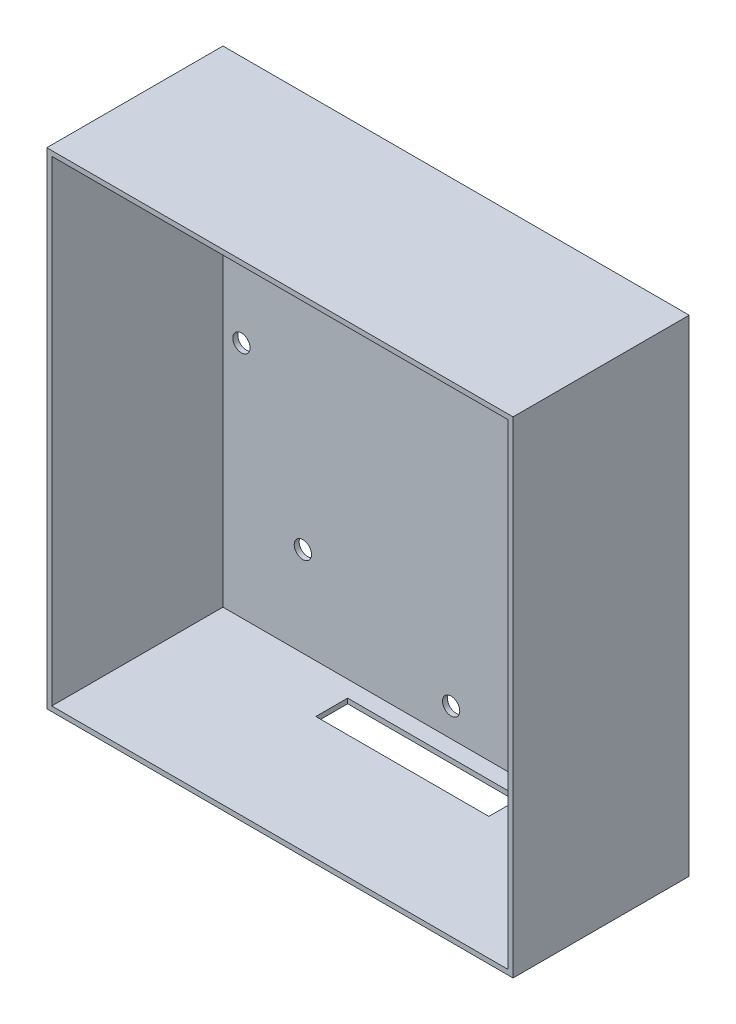
SolidWorks part; units mm, degrees
ref_plane "前视基准面" through (0, 0, 0) normal (0, 0, 1) x (1, 0, 0)
ref_plane "上视基准面" through (0, 0, 0) normal (0, 1, 0) x (1, 0, 0)
ref_plane "右视基准面" through (0, 0, 0) normal (1, 0, 0) x (0, 0, -1)
other "Configuration Table"
sketch "草图2" plane through (0, 0, 0) normal (0, 0, 1) x (1, 0, 0)
  line L0 (94.5, 49.25) -> (0, 49.25) construction
  line L1 (0, 0) -> (94.5, 0)
  line L2 (0, 0) -> (0, 98.5)
  line L3 (0, 98.5) -> (94.5, 98.5)
  line L4 (94.5, 0) -> (94.5, 98.5)
  line L5 (47.25, 98.5) -> (47.25, 0) construction
  dimension "D1" = 94.5
  dimension "D2" = 98.5
extrude "凸台-拉伸1" add sketch "草图2" along normal blind 35.7
shell "抽壳1" thickness 1
sketch "草图3" plane through (0, 0, 1) normal (0, 0, 1) x (1, 0, 0)
  line L0 (200094.5, 49.25) -> (-200000, 49.25) construction
  line L1 (47.25, 200098.5) -> (47.25, -200000) construction
  line L2 (47.25, 49.25) -> (4.75, 49.25) construction
  line L3 (47.25, 49.25) -> (17.198, 19.198) construction
  circle A0 centre (4.75, 49.25) radius 1.75
  circle A1 centre (17.198, 19.198) radius 1.75
  circle A2 centre (47.25, 6.75) radius 1.75
  circle A3 centre (77.302, 19.198) radius 1.75
  circle A4 centre (89.75, 49.25) radius 1.75
  circle A5 centre (77.302, 79.302) radius 1.75
  circle A6 centre (47.25, 91.75) radius 1.75
  circle A7 centre (17.198, 79.302) radius 1.75
  point P6 (47.25, 49.25)
  dimension "D1" = 42.5
  dimension "D3" = 45
  dimension "D2" = 8
sketch "草图5" plane through (0, 1, 0) normal (0, 1, 0) x (1, 0, 0)
  line L1 (0, -17.85) -> (93.5, -17.85) construction
  line L5 (47.145, 0) -> (47.145, -32.6168) construction
  line L8 (29.6066, -10.7814) -> (64.6834, -10.7814)
  line L9 (29.6066, -10.7814) -> (29.6066, -4.3298)
  line L10 (29.6066, -4.3298) -> (64.6834, -4.3298)
  line L11 (64.6834, -10.7814) -> (64.6834, -4.3298)
  line L12 (29.6066, -10.7814) -> (64.6834, -4.3298) construction
  line L13 (29.6066, -4.3298) -> (64.6834, -10.7814) construction
  point P0 (47.145, -7.5556)
  point P9 (0, 0)
  point P10 (0, 0)
  point P11 (0, 0)
  point P12 (64.7048, -9.393)
  point P13 (0, 0)
  point P14 (64.6834, -10.7814)
extrude "切除-拉伸1" cut sketch "草图5" against normal through all
extrude "切除-拉伸2" cut sketch "草图3" against normal through all
